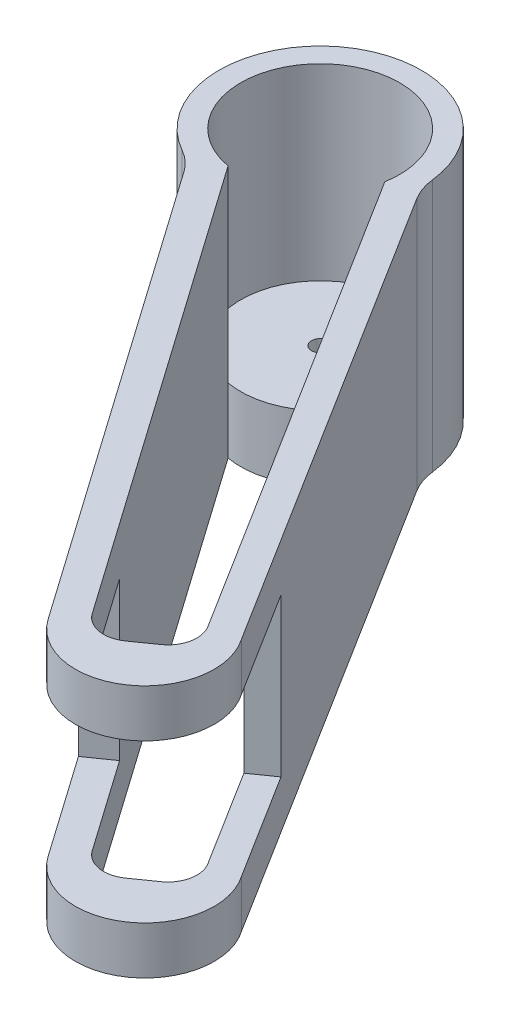
SolidWorks part; units mm, degrees
ref_plane "Front Plane" through (0, 0, 0) normal (0, 0, 1) x (1, 0, 0)
ref_plane "Top Plane" through (0, 0, 0) normal (0, 1, 0) x (1, 0, 0)
ref_plane "Right Plane" through (0, 0, 0) normal (1, 0, 0) x (0, 0, -1)
sketch "Sketch1" plane through (0, 0, 0) normal (0, 1, 0) x (1, 0, 0)
  line L0 (-5.4363, -18.4845) -> (50.7539, -98.5509)
  line L1 (19.1439, -2.1776) -> (70.7276, -84.5334)
  line L2 (-9.8292, 14.816) -> (72.0116, -108.5463) construction
  arc A0 (17.6619, 2.0463) -> (-8.7517, -15.4769) centre (0, 0) ccw
  arc A1 (-5.4363, -18.4845) -> (-8.7517, -15.4769) centre (-13.7527, -24.3209) ccw
  arc A2 (19.1439, -2.1776) -> (17.6619, 2.0463) centre (27.7543, 3.2156) cw
  arc A3 (50.7539, -98.5509) -> (70.7276, -84.5334) centre (60.7407, -91.5421) ccw
  point P10 (17.78, 0)
  dimension "D1" = 35.56
  dimension "D2" = 10.16
  dimension "D3" = 10.16
  dimension "D4" = 1.5
  dimension "D5" = 1.5
extrude "Boss-Extrude1" add sketch "Sketch1" along normal blind 44.45
sketch "Sketch2" plane through (0, 44.45, 0) normal (0, 1, 0) x (1, 0, 0)
  circle A0 centre (0, 0) radius 13.97
  dimension "D1" = 27.94
extrude "Cut-Extrude1" cut sketch "Sketch2" against normal blind 33.02
sketch "Sketch4" plane through (0, 0, 0) normal (0, -1, 0) x (1, 0, 0)
  circle A0 centre (0, 0) radius 1.524
  dimension "D1" = 3.048
extrude "Cut-Extrude2" cut sketch "Sketch4" against normal blind 11.43
sketch "Sketch5" plane through (0, 44.45, 0) normal (0, 1, 0) x (1, 0, 0)
  line L0 (0, 0) -> (60.7407, -91.5421) construction
  line L1 (-2.42, -13.7588) -> (53.7613, -93.7995)
  line L6 (13.7613, -2.4058) -> (65.8871, -85.6131)
  line L7 (64.5006, -92.468) -> (60.8378, -95.0389)
  arc A0 (-2.42, -13.7588) -> (13.7613, -2.4058) centre (0, 0) ccw
  circle A1 centre (0, 0) radius 13.97 construction
  circle A2 centre (0, 0) radius 13.97 construction
  arc A15 (64.5006, -92.468) -> (65.8871, -85.6131) centre (61.5821, -88.31) ccw
  arc A16 (60.8378, -95.0389) -> (53.7613, -93.7995) centre (57.9193, -90.881) cw
  dimension "D4" = 5.08
  dimension "D5" = 5.08
  dimension "D2" = 1.5
  dimension "D3" = 1.5
extrude "Cut-Extrude4" cut sketch "Sketch5" against normal blind 44.45
ref_plane "Plane1" through (63.3117, 0, 90.1992) normal (-0.5745, 0, -0.8185) x (-0.8185, 0, 0.5745)
sketch "Sketch6" plane through (63.3117, 0, 90.1992) normal (-0.5745, 0, -0.8185) x (-0.8185, 0, 0.5745)
  line L0 (17.78, 44.45) -> (-17.78, 44.45) construction
  line L1 (-21.0292, 36.068) -> (23.7704, 36.068)
  line L2 (-21.0292, 36.068) -> (-21.0292, 8.382)
  line L3 (-21.0292, 8.382) -> (23.7704, 8.382)
  line L4 (23.7704, 36.068) -> (23.7704, 8.382)
  line L5 (-17.78, 0) -> (17.78, 0) construction
  dimension "D1" = 8.382
  dimension "D2" = 8.382
extrude "Cut-Extrude5" cut sketch "Sketch6" against normal mid plane 44.45
